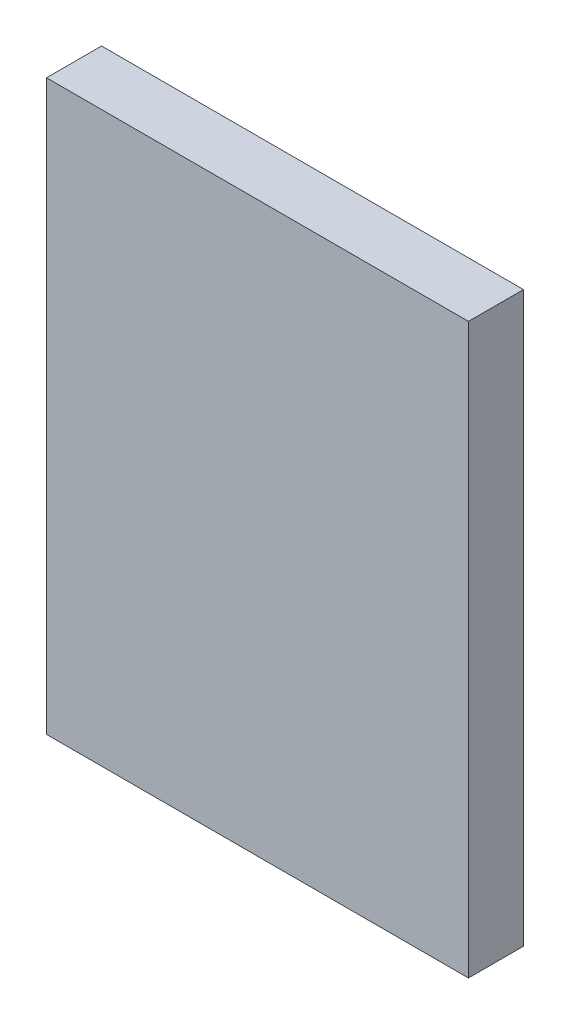
SolidWorks part; units mm, degrees
ref_plane "Plan de face" through (0, 0, 0) normal (0, 0, 1) x (1, 0, 0)
ref_plane "Plan de dessus" through (0, 0, 0) normal (0, 1, 0) x (1, 0, 0)
ref_plane "Plan de droite" through (0, 0, 0) normal (1, 0, 0) x (0, 0, -1)
sketch "Esquisse1" plane through (0, 0, 0) normal (0, 0, 1) x (1, 0, 0)
  line L1 (-11.5, 15.5) -> (11.5, 15.5)
  line L2 (-11.5, 15.5) -> (-11.5, -15.5)
  line L3 (-11.5, -15.5) -> (11.5, -15.5)
  line L4 (11.5, 15.5) -> (11.5, -15.5)
  line L5 (-11.5, 15.5) -> (11.5, -15.5) construction
  line L6 (-11.5, -15.5) -> (11.5, 15.5) construction
  point P0 (0, 0)
  dimension "D1" = 31
  dimension "D2" = 23
extrude "Boss.-Extru.1" add sketch "Esquisse1" along normal blind 3
